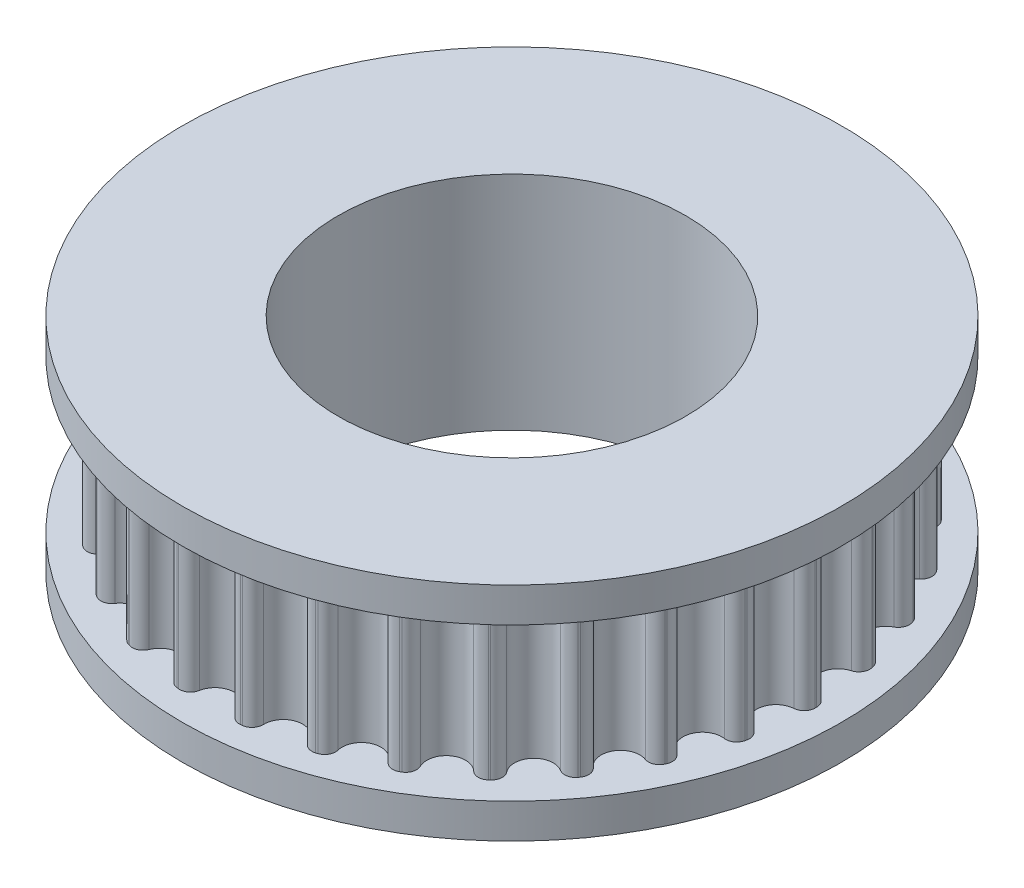
SolidWorks part; units mm, degrees
ref_plane "Front Plane" through (0, 0, 0) normal (0, 0, 1) x (1, 0, 0)
ref_plane "Top Plane" through (0, 0, 0) normal (0, 1, 0) x (1, 0, 0)
ref_plane "Right Plane" through (0, 0, 0) normal (1, 0, 0) x (0, 0, -1)
sketch "Sketch1" plane through (0, 0, 0) normal (0, 1, 0) x (1, 0, 0)
  line L0 (0, 0) -> (0, 13.9424) construction
  line L1 (0, 0) -> (2.8302, 13.3149) construction
  circle A0 centre (0, 0) radius 13.9424 construction
  circle A1 centre (0, 0) radius 12.7224 construction
  circle A2 centre (0, 13.6124) radius 0.89 construction
  circle A5 centre (2.8302, 13.3149) radius 0.89 construction
  arc A6 (0, 12.7224) -> (0.8766, 13.4588) centre (0, 13.6124) ccw
  arc A7 (0.8766, 13.4588) -> (1.4201, 13.8699) centre (1.3691, 13.3725) cw
  arc A8 (1.4947, 13.862) -> (1.9407, 13.3469) centre (1.4411, 13.3649) cw
  arc A9 (2.6451, 12.4444) -> (1.9407, 13.3469) centre (2.8302, 13.3149) cw
  arc A10 (1.4201, 13.8699) -> (1.4947, 13.862) centre (0, 0) cw
  arc A11 (0, 12.7224) -> (2.6451, 12.4444) centre (0, 0) ccw
  dimension "D1" = 27.8847
  dimension "D3" = 1.78
  dimension "D4" = 0.5
  dimension "D5" = 12
extrude "Boss-Extrude1" add sketch "Sketch1" along normal mid plane 7 contours A6 A11 A9 A8 A7
ref_axis "Axis1" through (0, 3.3, 0) along (0, -1, 0)
pattern_circular "CirPattern1" count 30 over 360 about axis through (0, 0, 0) along (0, 1, 0) of "Boss-Extrude1"
sketch "Sketch2" plane through (0, 0, 0) normal (1, 0, 0) x (0, 0, -1)
  line L10 (0, 3.5) -> (15.1171, 3.5) construction
  line L11 (0, 3.5) -> (0, 5.0875) construction
  line L12 (0, 5.0875) -> (15.1171, 5.0875) construction
  line L15 (15.1171, 3.5) -> (15.1171, 5.0875) construction
  line L20 (0, 3.3) -> (0, -3.3) construction
  line L22 (15.1171, 5.0875) -> (0, 5.0875)
  line L23 (15.1171, 5.0875) -> (15.1171, 3.5)
  line L24 (15.1171, 3.5) -> (0, 3.5)
  line L25 (0, 5.0875) -> (0, 3.5)
  dimension "D1" = 1.5875
  dimension "D2" = 15.1171
  dimension "D3" = 3.5
revolve "Revolve3" add sketch "Sketch2" angle 360 about axis through (0, 3.3, 0) along (0, -1, 0)
mirror "Mirror1" about plane through (0, 0, 0) normal (0, 1, 0) of "Revolve3"
sketch "Sketch3" plane through (0, 0, 0) normal (0, -1, 0) x (-1, 0, 0)
  circle A0 centre (0, 0) radius 7.9734
  dimension "D1" = 15.9467
extrude "Cut-Extrude1" cut sketch "Sketch3" against normal through all both and the other way through all
equation "\"TEETH_NUM\"= 30"
equation "\"TOOTH_PITCH\"= 3mm"
equation "\"PITCH_LINE_OFFSET\"= .015in"
equation "\"DIAMETER_PER_GROOVE\"= \"OUTSIDE_DIAMETER\" / \"TEETH_NUM\" * 1in"
equation "\"PITCH_DIAMETER\"= ( ( \"TEETH_NUM\" * 3 - 1.31 ) / 3.1415 + .415 ) * 1mm"
equation "\"OUTSIDE_DIAMETER\"= \"PITCH_DIAMETER\" - \"PITCH_LINE_OFFSET\" * 2"
equation "\"D1@Sketch1\"=\"OUTSIDE_DIAMETER\""
equation "\"TOOTH_HEIGHT\"= 1.22mm"
equation "\"D2@Sketch1\"=\"TOOTH_HEIGHT\""
equation "\"TOOTH_DIAMETER\"= 1.78mm"
equation "\"INTERNAL_RADIUS\"= .5mm"
equation "\"D3@Sketch1\"=\"TOOTH_DIAMETER\""
equation "\"D5@Sketch1\"=360 / \"TEETH_NUM\""
equation "\"D4@Sketch1\"=\"INTERNAL_RADIUS\""
equation "\"D1@CirPattern1\"=\"TEETH_NUM\""
equation "\"BELT_GAP\"= 7mm"
equation "\"D2@Sketch2\"=\"PITCH_DIAMETER\"/2+1/32"
equation "\"D3@Sketch2\"=\"BELT_GAP\"/2"
equation "\"D1@Sketch3\"=\"PITCH_DIAMETER\"-.5"
equation "\"D1@Boss-Extrude1\"=\"BELT_GAP\""
